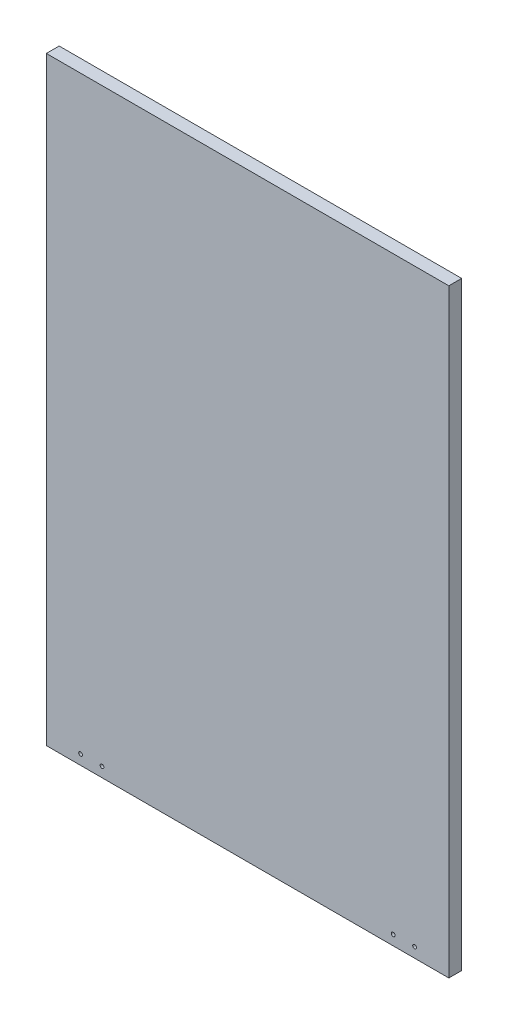
SolidWorks part; units mm, degrees
ref_plane "Front Plane" through (0, 0, 0) normal (0, 0, 1) x (1, 0, 0)
ref_plane "Top Plane" through (0, 0, 0) normal (0, 1, 0) x (1, 0, 0)
ref_plane "Right Plane" through (0, 0, 0) normal (1, 0, 0) x (0, 0, -1)
sketch "Sketch1" plane through (0, 0, 0) normal (0, 0, 1) x (1, 0, 0)
  line L1 (-235, 350) -> (235, 350)
  line L2 (-235, 350) -> (-235, -350)
  line L3 (-235, -350) -> (235, -350)
  line L4 (235, 350) -> (235, -350)
  line L5 (-235, 350) -> (235, -350) construction
  line L6 (-235, -350) -> (235, 350) construction
  circle A0 centre (-195, -338.4) radius 2.2
  circle A1 centre (195, -338.4) radius 2.2
  circle A2 centre (-170, -338.4) radius 2.2
  circle A3 centre (170, -338.4) radius 2.2
  point P0 (0, 0)
  dimension "D3" = 4.4
  dimension "D7" = 2
  dimension "D1" = 470
  dimension "D2" = 700
  dimension "D4" = 40
  dimension "D5" = 11.6
  dimension "D6" = 40
  dimension "D8" = 25
  dimension "D10" = 25
  dimension "D9" = 2
extrude "Boss-Extrude1" add sketch "Sketch1" along normal blind 15
